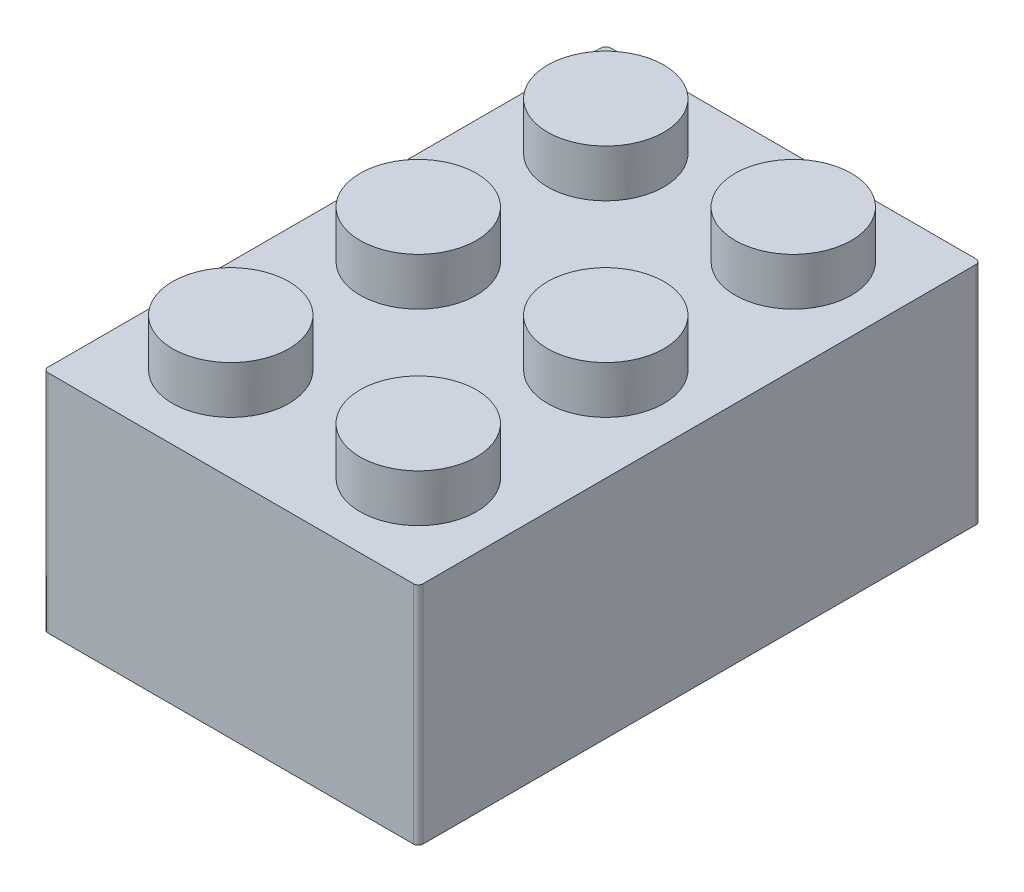
SolidWorks part; units mm, degrees
ref_plane "Front Plane" through (0, 0, 0) normal (0, 0, 1) x (1, 0, 0)
ref_plane "Top Plane" through (0, 0, 0) normal (0, 1, 0) x (1, 0, 0)
ref_plane "Right Plane" through (0, 0, 0) normal (1, 0, 0) x (0, 0, -1)
sketch "stencil" plane through (0, 0, 0) normal (0, 1, 0) x (1, 0, 0)
  line L2 (14.3, 22.2) -> (1.5, 22.2)
  line L29 (15.8, 23.7) -> (0, 23.7)
  line L37 (15.8, 23.7) -> (15.8, 0)
  line L38 (15.8, 0) -> (0, 0)
  line L39 (0, 23.7) -> (0, 0)
  line L40 (7.9, 0) -> (7.9, 23.7) construction
  line L41 (15.8, 11.85) -> (0, 11.85) construction
  line L50 (1.5, 22.2) -> (1.5, 1.5)
  line L51 (14.3, 1.5) -> (1.5, 1.5)
  line L52 (14.3, 22.2) -> (14.3, 1.5)
  circle A43 centre (3.95, 3.95) radius 2.45
  circle A44 centre (7.9, 7.9) radius 3.25
  circle A46 centre (3.95, 11.85) radius 2.45
  circle A47 centre (7.9, 15.8) radius 3.25
  circle A49 centre (3.95, 19.75) radius 2.45
  circle A50 centre (11.85, 19.75) radius 2.45
  circle A51 centre (11.85, 11.85) radius 2.45
  circle A52 centre (11.85, 3.95) radius 2.45
  circle A53 centre (7.9, 15.8) radius 2.45
  circle A54 centre (7.9, 7.9) radius 2.45
  point P1 (0, 0)
  point P6 (3.95, -15.8)
  point P9 (7.9, -15.8)
  point P10 (7.9, -11.85)
  point P13 (3.95, -7.9)
  point P15 (7.9, -7.9)
  point P17 (7.9, -3.95)
  point P18 (3.95, 0)
  point P21 (7.9, 0)
  point P25 (7.9, 3.95)
  point P27 (3.95, 7.9)
  point P28 (7.9, 7.9)
  point P29 (0, -11.85)
  point P30 (0, -7.9)
  point P31 (0, 3.95)
  point P34 (0, -3.95)
  point P35 (3.95, 0)
  point P36 (0, 15.8)
  point P37 (0, 23.7)
  point P38 (7.9, 23.7)
  point P39 (15.8, 23.7)
  point P40 (15.8, 15.8)
  point P41 (15.8, 7.9)
  point P48 (15.8, 0)
  point P49 (7.9, 0)
  point P51 (11.85, 0)
  point P52 (3.95, 3.95)
  point P53 (7.9, 3.95)
  point P55 (11.85, 3.95)
  point P56 (3.95, 7.9)
  point P57 (7.9, 7.9)
  point P58 (11.85, 7.9)
  point P59 (3.95, 11.85)
  point P60 (7.9, 11.85)
  point P61 (11.85, 11.85)
  point P64 (3.95, 15.8)
  point P65 (7.9, 15.8)
  point P66 (11.85, 15.8)
  point P68 (3.95, 19.75)
  point P69 (7.9, 19.75)
  point P70 (11.85, 19.75)
  point P71 (0, 3.95)
  point P73 (0, 7.9)
  point P75 (0, 11.85)
  point P77 (0, 15.8)
  point P79 (0, 19.75)
  point P81 (15.8, 3.95)
  point P83 (15.8, 7.9)
  point P85 (15.8, 11.85)
  point P87 (15.8, 15.8)
  point P88 (15.8, 19.75)
  point P91 (0, 23.7)
  point P93 (3.95, 23.7)
  point P94 (7.9, 23.7)
  point P95 (11.85, 23.7)
  point P96 (15.8, 23.7)
  point P97 (7.9, 11.85)
  point P118 (7.9, 11.85)
  dimension "D5" = 4.9
  dimension "D7" = 6.5
  dimension "D3" = 3.95
  dimension "D4" = 3.95
  dimension "D9" = 23.7
  dimension "D10" = 15.8
  dimension "D6" = 0.8
  dimension "D8" = 0.8
  dimension "D11" = 1.5
  dimension "D1" = 5
  dimension "D2" = 7
sketch "Sketch1" plane through (0, 0, 0) normal (0, 1, 0) x (1, 0, 0)
  line L9 (15.8, 23.7) -> (0, 23.7)
  line L10 (15.8, 23.7) -> (15.8, 0)
  line L11 (15.8, 0) -> (0, 0)
  line L12 (0, 23.7) -> (0, 0)
  line L13 (7.9, 0) -> (7.9, 23.7) construction
  line L14 (15.8, 11.85) -> (0, 11.85) construction
  point P0 (7.9, 11.85)
extrude "Boss-Extrude1" add sketch "Sketch1" along normal mid plane 9.5
sketch "Sketch2" plane through (0, 4.75, 0) normal (0, 1, 0) x (1, 0, 0)
  circle A14 centre (3.95, 3.95) radius 2.45
  circle A15 centre (11.85, 3.95) radius 2.45
  circle A16 centre (11.85, 11.85) radius 2.45
  circle A17 centre (3.95, 11.85) radius 2.45
  circle A18 centre (3.95, 19.75) radius 2.45
  circle A19 centre (11.85, 19.75) radius 2.45
  circle A20 centre (3.95, 3.95) radius 2.45 construction
extrude "Boss-Extrude2" add sketch "Sketch2" along normal blind 2
sketch "Sketch4" plane through (0, -4.75, 0) normal (0, -1, 0) x (1, 0, 0)
  line L5 (14.3, -22.2) -> (1.5, -22.2)
  line L7 (14.3, -22.2) -> (14.3, -1.5)
  line L11 (14.3, -1.5) -> (1.5, -1.5)
  line L12 (1.5, -22.2) -> (1.5, -1.5)
  line L13 (7.9, -1.5) -> (7.9, -22.2) construction
  line L14 (14.3, -11.85) -> (1.5, -11.85) construction
  point P0 (7.9, -11.85)
extrude "Cut-Extrude1" cut sketch "Sketch4" against normal blind 4
sketch "Sketch5" plane through (0, -0.75, 0) normal (0, -1, 0) x (1, 0, 0)
  circle A1 centre (7.9, -7.9) radius 2.45
  circle A5 centre (7.9, -15.8) radius 2.45
  circle A12 centre (7.9, -15.8) radius 3.25
  circle A13 centre (7.9, -7.9) radius 3.25
  circle A14 centre (7.9, -15.8) radius 2.45 construction
  circle A15 centre (7.9, -7.9) radius 3.25 construction
extrude "Boss-Extrude3" add sketch "Sketch5" along normal up to surface (4 mm away) up to face at (7.9, -4.75, -11.85)
fillet "Fillet1" radius 0.2 4 edges at (0, 0, -23.7) (15.8, 0, -23.7) (0, 0, 0) (15.8, 0, 0)
equation "\"t\"= 0.0'tolerance"
equation "\"D9@stencil\"=23.70-\"t\""
equation "\"D10@stencil\"=15.80-\"t\""
equation "\"D11@stencil\"=1.50-\"t\""
equation "\"D7@stencil\"=6.50-\"t\""
